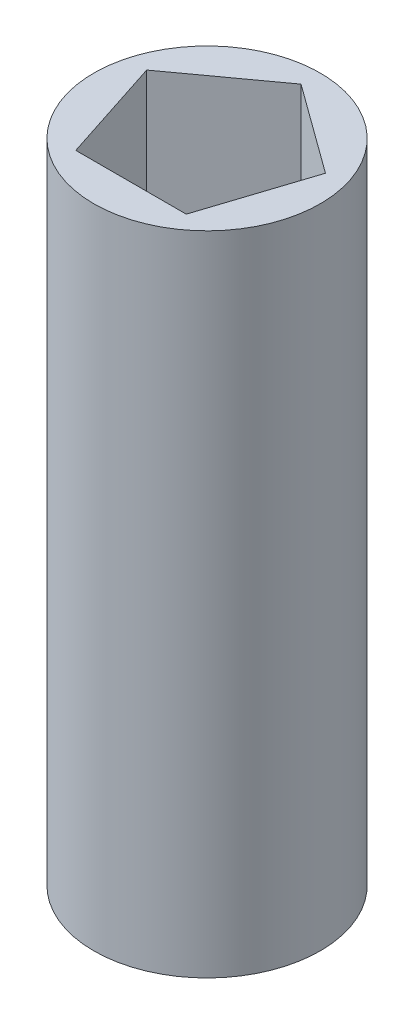
SolidWorks part; units mm, degrees
ref_plane "Front Plane" through (0, 0, 0) normal (0, 0, 1) x (1, 0, 0)
ref_plane "Top Plane" through (0, 0, 0) normal (0, 1, 0) x (1, 0, 0)
ref_plane "Right Plane" through (0, 0, 0) normal (1, 0, 0) x (0, 0, -1)
sketch "Sketch1" plane through (0, 0, 0) normal (0, 1, 0) x (1, 0, 0)
  line L1 (1.7074, -2.35) -> (2.7626, 0.8976)
  line L2 (2.7626, 0.8976) -> (0, 2.9048)
  line L3 (0, 2.9048) -> (-2.7626, 0.8976)
  line L4 (-2.7626, 0.8976) -> (-1.7074, -2.35)
  line L5 (-1.7074, -2.35) -> (1.7074, -2.35)
  circle A0 centre (0, 0) radius 3.5
  circle A1 centre (0, 0) radius 2.35 construction
  dimension "D1" = 4.7
  dimension "D2" = 7
extrude "Boss-Extrude1" add sketch "Sketch1" along normal blind 20
